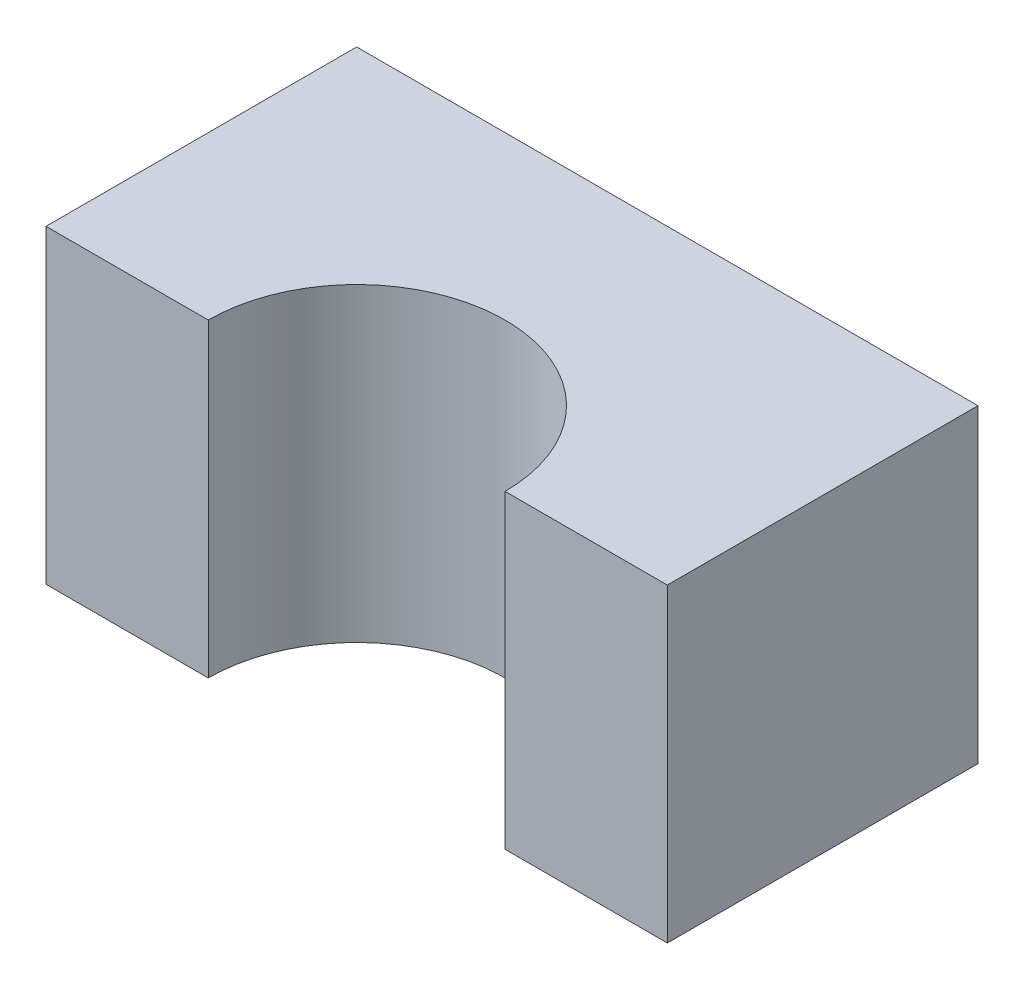
SolidWorks part; units mm, degrees
ref_plane "Front Plane" through (0, 0, 0) normal (0, 0, 1) x (1, 0, 0)
ref_plane "Top Plane" through (0, 0, 0) normal (0, 1, 0) x (1, 0, 0)
ref_plane "Right Plane" through (0, 0, 0) normal (1, 0, 0) x (0, 0, -1)
sketch "Sketch2" plane through (0, 0, 0) normal (0, 0, 1) x (1, 0, 0)
  line L1 (-39.878, 19.8975) -> (39.878, 19.8975)
  line L2 (-39.878, 19.8975) -> (-39.878, -19.8975)
  line L3 (-39.878, -19.8975) -> (39.878, -19.8975)
  line L4 (39.878, 19.8975) -> (39.878, -19.8975)
  line L5 (-39.878, 19.8975) -> (39.878, -19.8975) construction
  line L6 (-39.878, -19.8975) -> (39.878, 19.8975) construction
  point P0 (0, 0)
  dimension "D1" = 79.756
  dimension "D2" = 39.7951
extrude "Boss-Extrude1" add sketch "Sketch2" against normal blind 39.878
sketch "Sketch4" plane through (0, 19.8975, 0) normal (0, 1, 0) x (1, 0, 0)
  circle A0 centre (0, 0) radius 19.05
  point P2 (0, 2.5803)
  point P3 (0, 0)
  point P4 (0, 0)
  dimension "D1" = 38.1
extrude "Cut-Extrude2" cut sketch "Sketch4" against normal through all both contours A0
